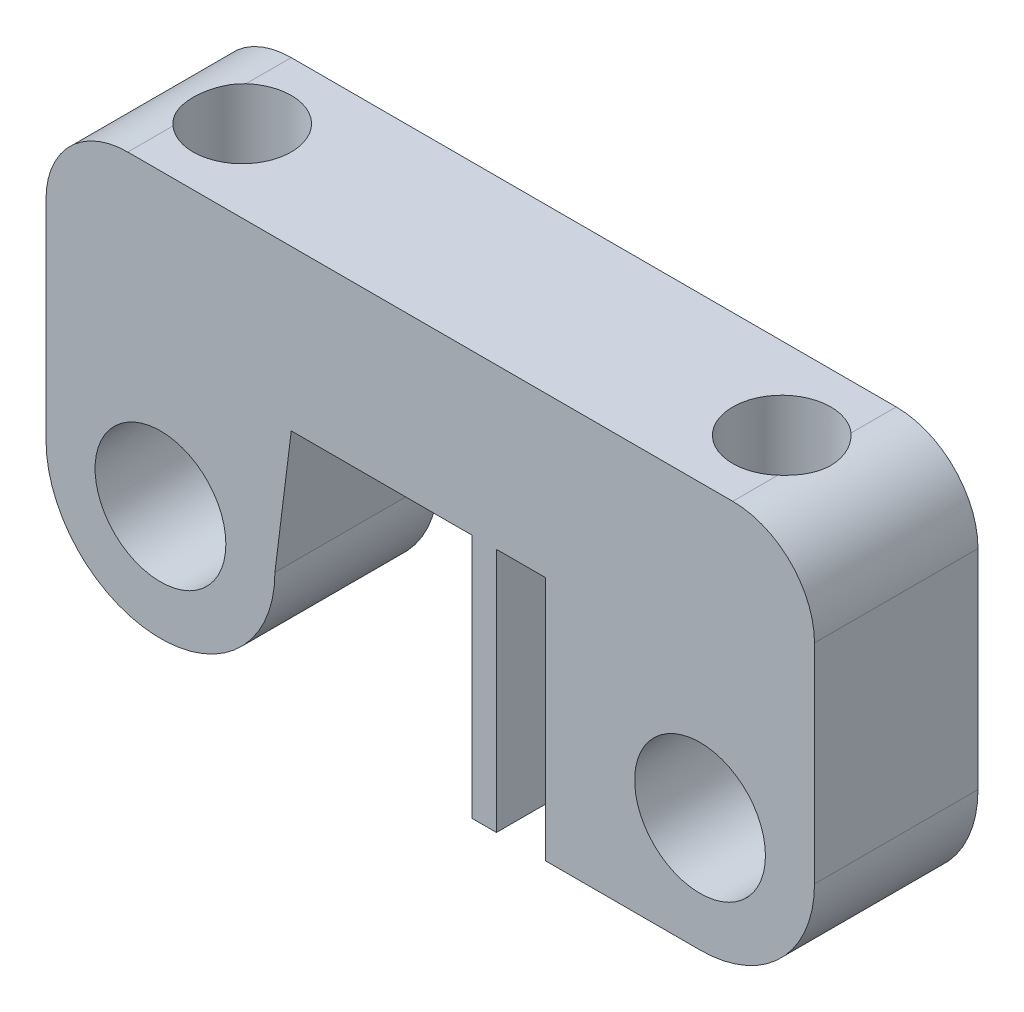
SolidWorks part; units mm, degrees
material "ABS"
ref_plane "Plano frontal" through (0, 0, 0) normal (0, 0, 1) x (1, 0, 0)
ref_plane "Plano superior" through (0, 0, 0) normal (0, 1, 0) x (1, 0, 0)
ref_plane "Plano direito" through (0, 0, 0) normal (1, 0, 0) x (0, 0, -1)
sketch "Esboço1" plane through (0, 0, 0) normal (0, 0, 1) x (1, 0, 0)
  line L0 (-16.5, 0) -> (16.5, 0) construction
  line L1 (-23.5, 0) -> (-23.5, 12.7669)
  line L2 (-9.5, 0) -> (-8.5, 8)
  line L3 (-8.5, 8) -> (2.5478, 8)
  line L4 (4.0478, 8) -> (7.0478, 8)
  line L5 (-18.5, 17.7669) -> (18.5, 17.7669)
  line L6 (23.5, 12.7669) -> (23.5, 0)
  line L7 (7.0478, 8) -> (7.0478, -7)
  line L8 (4.0478, 8) -> (4.0478, -7)
  line L9 (4.0478, -7) -> (2.5478, -7)
  line L10 (2.5478, -7) -> (2.5478, 8)
  line L11 (7.0478, -7) -> (16.5, -7)
  arc A0 (-23.5, 0) -> (-9.5, 0) centre (-16.5, 0) ccw
  arc A1 (16.5, -7) -> (23.5, 0) centre (16.5, 0) ccw
  circle A2 centre (-16.5, 0) radius 4
  circle A3 centre (16.5, 0) radius 4
  arc A4 (18.5, 17.7669) -> (23.5, 12.7669) centre (18.5, 12.7669) cw
  arc A5 (-23.5, 12.7669) -> (-18.5, 17.7669) centre (-18.5, 12.7669) cw
  point P4 (0, 0)
  dimension "D1" = 8
  dimension "D2" = 8
  dimension "D4" = 1.5
  dimension "D3" = 33
  dimension "D6" = 14
  dimension "D7" = 14
  dimension "D8" = 8
  dimension "D10" = 5
  dimension "D5" = 8
  dimension "D9" = 3
extrude "Ressalto-extrusão1" add sketch "Esboço1" along normal blind 10
sketch "Esboço6" plane through (0, 0, 0) normal (0, 0, -1) x (-1, 0, 0)
  line L0 (-7.0478, -7) -> (-12.8584, -4.7307) construction
  point P3 (-12.8584, -4.7307)
sketch "Esboço2" plane through (2.5478, 0, 0) normal (-1, 0, 0) x (0, 0, 1)
  line L0 (5, -7) -> (5, -2.2586) construction
  line L1 (10, -7) -> (0, -7) construction
  circle A0 centre (5, -5.2286) radius 1
  point P6 (5, -5.2286)
  dimension "D1" = 2
extrude "Corte-extrusão1" cut sketch "Esboço2" along direction (0.9315, 0.3638, 0) on the side against the normal blind 10
sketch "Esboço3" plane through (0, 17.7669, 0) normal (0, 1, 0) x (1, 0, 0)
  line L0 (-16.5, 0) -> (-16.5, -10) construction
  line L1 (-12.5, 0) -> (-20.5, 0) construction
  line L2 (18.5, -10) -> (-18.5, -10) construction
  line L4 (16.5, 0) -> (16.5, -10) construction
  circle A0 centre (-16.5, -5) radius 1
  circle A1 centre (16.5, -5) radius 1
  dimension "D1" = 2
extrude "Corte-extrusão2" cut sketch "Esboço3" against normal blind 20
sketch "Esboço5" plane through (0, 17.7669, 0) normal (0, 1, 0) x (1, 0, 0)
  circle A0 centre (-16.5, -5) radius 3
  circle A1 centre (16.5, -5) radius 3
  dimension "D1" = 6
extrude "Corte-extrusão3" cut sketch "Esboço5" against normal blind 6
